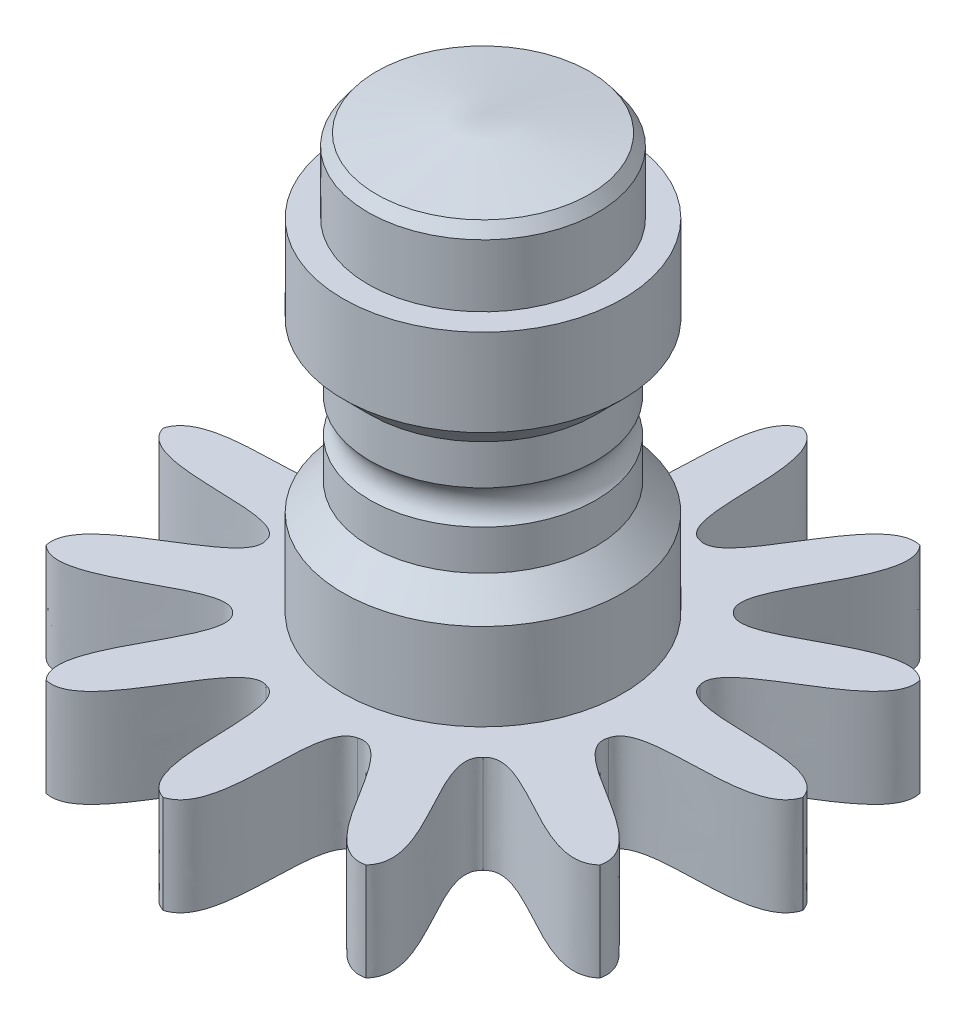
SolidWorks part; units mm, degrees
ref_plane "Alzado" through (0, 0, 0) normal (0, 0, 1) x (1, 0, 0)
ref_plane "Planta" through (0, 0, 0) normal (0, 1, 0) x (1, 0, 0)
ref_plane "Vista lateral" through (0, 0, 0) normal (1, 0, 0) x (0, 0, -1)
sketch "Sketch1" plane through (0, 0, 0) normal (0, 1, 0) x (1, 0, 0)
  line L0 (0, -1000) -> (0, 49000) construction
  line L1 (0, 0) -> (12940.9523, 48296.2913) construction
  circle A0 centre (0, 0) radius 1.6 construction
  circle A1 centre (0, 0) radius 0.8865 construction
  spline S0 degree 3 poles (0, 1.6) (0.2312, 1.532) (0.0492, 0.8903) (0.2294, 0.8563) knots 0 0 0 0 1 1 1 1
  spline S1 degree 3 poles (0, 1.6) (-0.2312, 1.532) (-0.0492, 0.8903) (-0.2294, 0.8563) knots 0 0 0 0 1 1 1 1
  spline S2 degree 3 poles (0.8, 1.3856) (0.5658, 1.4423) (0.4025, 0.7957) (0.2294, 0.8563) knots 0 0 0 0 1 1 1 1
  spline S3 degree 3 poles (0.8, 1.3856) (0.9662, 1.2111) (0.4878, 0.7464) (0.6269, 0.6269) knots 0 0 0 0 1 1 1 1
  spline S4 degree 3 poles (1.3856, 0.8) (1.2111, 0.9662) (0.7464, 0.4878) (0.6269, 0.6269) knots 0 0 0 0 1 1 1 1
  spline S5 degree 3 poles (1.3856, 0.8) (1.4423, 0.5658) (0.7957, 0.4025) (0.8563, 0.2294) knots 0 0 0 0 1 1 1 1
  spline S6 degree 3 poles (1.6, 0) (1.532, 0.2312) (0.8903, 0.0492) (0.8563, 0.2294) knots 0 0 0 0 1 1 1 1
  spline S7 degree 3 poles (1.6, 0) (1.532, -0.2312) (0.8903, -0.0492) (0.8563, -0.2294) knots 0 0 0 0 1 1 1 1
  spline S8 degree 3 poles (1.3856, -0.8) (1.4423, -0.5658) (0.7957, -0.4025) (0.8563, -0.2294) knots 0 0 0 0 1 1 1 1
  spline S9 degree 3 poles (1.3856, -0.8) (1.2111, -0.9662) (0.7464, -0.4878) (0.6269, -0.6269) knots 0 0 0 0 1 1 1 1
  spline S10 degree 3 poles (0.8, -1.3856) (0.9662, -1.2111) (0.4878, -0.7464) (0.6269, -0.6269) knots 0 0 0 0 1 1 1 1
  spline S11 degree 3 poles (0.8, -1.3856) (0.5658, -1.4423) (0.4025, -0.7957) (0.2294, -0.8563) knots 0 0 0 0 1 1 1 1
  spline S12 degree 3 poles (0, -1.6) (0.2312, -1.532) (0.0492, -0.8903) (0.2294, -0.8563) knots 0 0 0 0 1 1 1 1
  spline S13 degree 3 poles (0, -1.6) (-0.2312, -1.532) (-0.0492, -0.8903) (-0.2294, -0.8563) knots 0 0 0 0 1 1 1 1
  spline S14 degree 3 poles (-0.8, -1.3856) (-0.5658, -1.4423) (-0.4025, -0.7957) (-0.2294, -0.8563) knots 0 0 0 0 1 1 1 1
  spline S15 degree 3 poles (-0.8, -1.3856) (-0.9662, -1.2111) (-0.4878, -0.7464) (-0.6269, -0.6269) knots 0 0 0 0 1 1 1 1
  spline S16 degree 3 poles (-1.3856, -0.8) (-1.2111, -0.9662) (-0.7464, -0.4878) (-0.6269, -0.6269) knots 0 0 0 0 1 1 1 1
  spline S17 degree 3 poles (-1.3856, -0.8) (-1.4423, -0.5658) (-0.7957, -0.4025) (-0.8563, -0.2294) knots 0 0 0 0 1 1 1 1
  spline S18 degree 3 poles (-1.6, 0) (-1.532, -0.2312) (-0.8903, -0.0492) (-0.8563, -0.2294) knots 0 0 0 0 1 1 1 1
  spline S19 degree 3 poles (-1.6, 0) (-1.532, 0.2312) (-0.8903, 0.0492) (-0.8563, 0.2294) knots 0 0 0 0 1 1 1 1
  spline S20 degree 3 poles (-1.3856, 0.8) (-1.4423, 0.5658) (-0.7957, 0.4025) (-0.8563, 0.2294) knots 0 0 0 0 1 1 1 1
  spline S21 degree 3 poles (-1.3856, 0.8) (-1.2111, 0.9662) (-0.7464, 0.4878) (-0.6269, 0.6269) knots 0 0 0 0 1 1 1 1
  spline S22 degree 3 poles (-0.8, 1.3856) (-0.9662, 1.2111) (-0.4878, 0.7464) (-0.6269, 0.6269) knots 0 0 0 0 1 1 1 1
  spline S23 degree 3 poles (-0.8, 1.3856) (-0.5658, 1.4423) (-0.4025, 0.7957) (-0.2294, 0.8563) knots 0 0 0 0 1 1 1 1
  point P4 (0, 1.6)
  point P9 (0.2294, 0.8563)
  point P49 (0, 0)
  dimension "D1" = 3.2
  dimension "D2" = 1.773
  dimension "D3" = 15
extrude "Boss-Extrude1 (12 teeth)" add sketch "Sketch1" along normal blind 0.49
sketch "Sketch2" plane through (0, 0.49, 0) normal (0, 1, 0) x (1, 0, 0)
  circle A0 centre (0, 0) radius 0.7
  dimension "D1" = 1.4
extrude "Boss-Extrude2" add sketch "Sketch2" along normal blind 1.71
sketch "Sketch3" plane through (0, 2.2, 0) normal (0, 1, 0) x (1, 0, 0)
  circle A0 centre (0, 0) radius 0.575
  dimension "D1" = 1.15
extrude "Boss-Extrude3" add sketch "Sketch3" along normal blind 0.45
chamfer "Chamfer1" distance 0.0875 distance2 0.575 1 edges at (0, 2.65, 0.575)
chamfer "Chamfer2" distance 0.0425 angle 45 1 edges at (0, 2.5625, 0.575)
sketch "Sketch4" plane through (0, 0, 0) normal (0, 0, 1) x (1, 0, 0)
  line L0 (0, 2.65) -> (-0.533, 2.5689)
  line L1 (0.533, 2.5689) -> (0, 2.65)
  line L2 (0.533, 2.5689) -> (0, 2.65) construction
  line L3 (0, 2.65) -> (-0.533, 2.5689) construction
  line L4 (-0.533, 2.5689) -> (-0.575, 2.5118)
  line L5 (0.575, 2.5118) -> (0.533, 2.5689)
  line L6 (0.575, 2.5118) -> (0.533, 2.5689) construction
  line L7 (-0.533, 2.5689) -> (-0.575, 2.5118) construction
  line L8 (-0.575, 2.2) -> (-0.575, 2.5118)
  line L9 (0.575, 2.5118) -> (0.575, 2.2)
  line L10 (0.575, 2.5118) -> (0.575, 2.2) construction
  line L11 (-0.575, 2.2) -> (-0.575, 2.5118) construction
  line L12 (0.7, 2.2) -> (0.575, 2.2)
  line L13 (-0.575, 2.2) -> (-0.7, 2.2)
  line L14 (-0.575, 2.2) -> (-0.7, 2.2) construction
  line L15 (0.7, 2.2) -> (0.575, 2.2) construction
  line L16 (-0.7, 0.49) -> (-0.7, 2.2)
  line L17 (0.7, 2.2) -> (0.7, 0.49)
  line L18 (0.7, 2.2) -> (0.7, 0.49) construction
  line L19 (-0.7, 0.49) -> (-0.7, 2.2) construction
  line L20 (0, -1000) -> (0, 49000) construction
  line L21 (-999.3, 0.49) -> (49000.7, 0.49) construction
  line L22 (-999.2381, 1.345) -> (49000.7619, 1.345) construction
  line L23 (0.565, -998.7923) -> (0.565, 49001.2077) construction
  line L24 (0.6497, -998.8059) -> (0.6497, 49001.1941) construction
  line L25 (-999.0038, 1.765) -> (49000.9962, 1.765) construction
  line L26 (-999.113, 0.925) -> (49000.887, 0.925) construction
  line L27 (0.7, 1.765) -> (35356.0391, 35357.1041) construction
  line L28 (0.7, 0.925) -> (-35354.6391, 35356.2641) construction
  line L29 (0.8111, 1.8761) -> (0.565, 1.63)
  line L30 (0.565, 1.26) -> (0.565, 1.06)
  line L31 (0.565, 1.63) -> (0.565, 1.43)
  line L33 (0.565, 1.06) -> (0.8111, 0.8139)
  line L34 (0.8111, 0.8139) -> (0.8111, 1.8761)
  arc A0 (0.565, 1.43) -> (0.565, 1.26) centre (0.6497, 1.345) ccw
  point P27 (0.7, 1.765)
  point P29 (0.7, 0.925)
  dimension "D4" = 0.12
  dimension "D1" = 0.855
  dimension "D2" = 0.6497
  dimension "D3" = 0.565
  dimension "D5" = 0.42
  dimension "D6" = 0.42
  dimension "D7" = 45
  dimension "D8" = 45
revolve "Cut-Revolve2" cut sketch "Sketch4" angle 360 about L20
sketch "Sketch5" plane through (0, 0, 0) normal (0, 0, 1) x (1, 0, 0)
  line L0 (0, -1000) -> (0, 49000) construction
  line L1 (0.375, -998.9054) -> (0.375, 49001.0946) construction
  line L2 (-999.9301, 2.28) -> (49000.0699, 2.28) construction
  line L3 (-1000, 0) -> (49000, 0) construction
  line L4 (0, 2.28) -> (43301.2702, -24997.72) construction
  line L5 (0, 0) -> (0, 2.28)
  line L6 (0, 2.28) -> (0.375, 2.0635)
  line L7 (0.375, 2.0635) -> (0.375, 0)
  line L8 (0.375, 0) -> (0, 0)
  point P8 (0, 2.28)
  dimension "D1" = 2.28
  dimension "D2" = 30
  dimension "D3" = 0.375
revolve "Cut-Revolve3" cut sketch "Sketch5" angle 360 about L0
